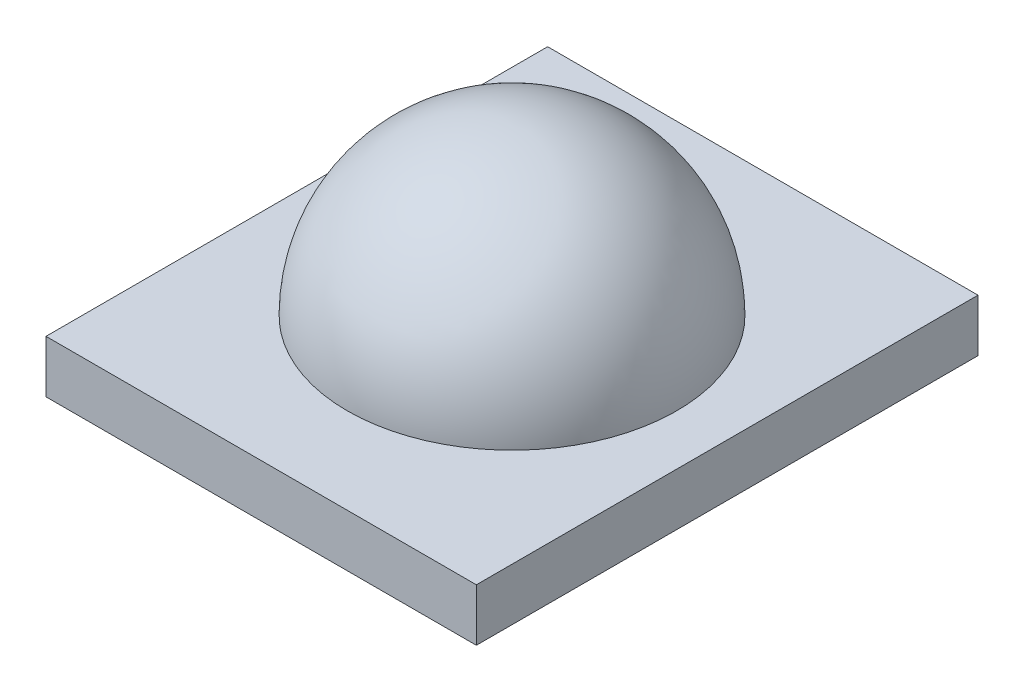
SolidWorks part; units mm, degrees
ref_plane "Front Plane" through (0, 0, 0) normal (0, 0, 1) x (1, 0, 0)
ref_plane "Top Plane" through (0, 0, 0) normal (0, 1, 0) x (1, 0, 0)
ref_plane "Right Plane" through (0, 0, 0) normal (1, 0, 0) x (0, 0, -1)
sketch "Sketch1" plane through (0, 0, 0) normal (0, 1, 0) x (1, 0, 0)
  line L1 (14.37, -16.75) -> (-14.37, -16.75)
  line L2 (14.37, -16.75) -> (14.37, 16.75)
  line L3 (14.37, 16.75) -> (-14.37, 16.75)
  line L4 (-14.37, -16.75) -> (-14.37, 16.75)
  line L5 (14.37, -16.75) -> (-14.37, 16.75) construction
  line L6 (14.37, 16.75) -> (-14.37, -16.75) construction
  point P0 (0, 0)
  dimension "D1" = 28.74
  dimension "D2" = 33.5
extrude "Boss-Extrude1" add sketch "Sketch1" along normal blind 3.5
sketch "Sketch3" plane through (0, 3.5, 0) normal (0, 1, 0) x (1, 0, 0)
  circle A0 centre (0, 0) radius 11
  dimension "D1" = 22
sketch "Sketch4" plane through (0, 0, 0) normal (1, 0, 0) x (0, 0, -1)
  line L0 (0, 0) -> (-11, 0)
  line L1 (-11, 0) -> (-11, 3.4)
  line L2 (0, 14.5005) -> (0, 0)
  arc A0 (-11, 3.4) -> (0, 14.5005) centre (0, 3.5) cw
  dimension "D1" = 11
  dimension "D2" = 3.4
revolve "Revolve1" add sketch "Sketch4" angle 360 about L2
